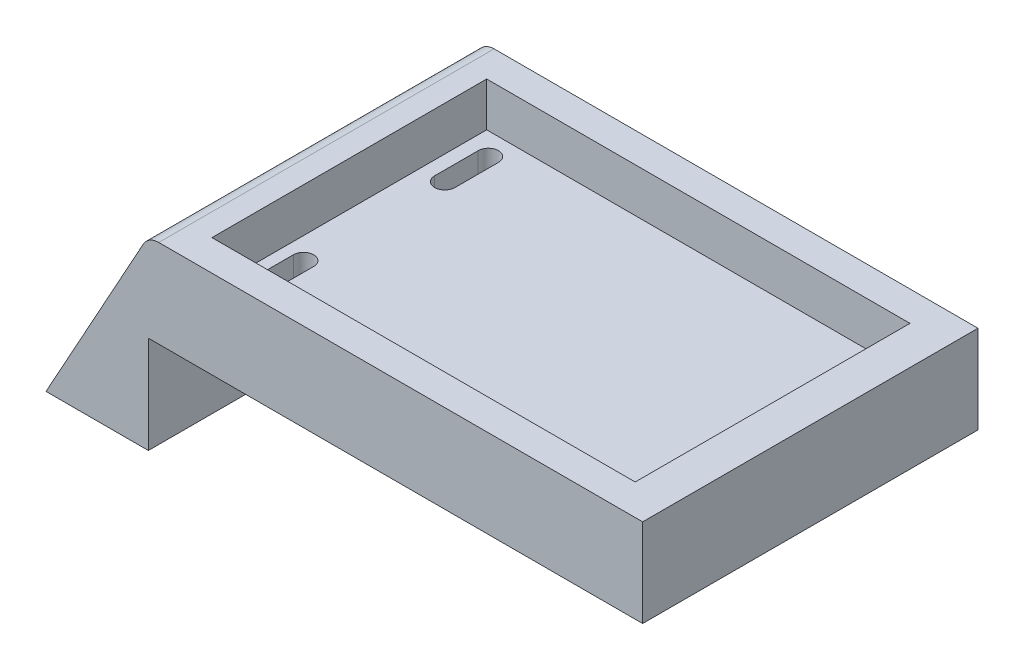
SolidWorks part; units mm, degrees
ref_plane "Front Plane" through (0, 0, 0) normal (0, 0, 1) x (1, 0, 0)
ref_plane "Top Plane" through (0, 0, 0) normal (0, 1, 0) x (1, 0, 0)
ref_plane "Right Plane" through (0, 0, 0) normal (1, 0, 0) x (0, 0, -1)
sketch "Sketch1" plane through (0, 0, 0) normal (0, 1, 0) x (1, 0, 0)
  line L1 (-34.7549, 21.5329) -> (36.5178, 21.5329)
  line L2 (-34.7549, 21.5329) -> (-34.7549, -26.8217)
  line L3 (-34.7549, -26.8217) -> (36.5178, -26.8217)
  line L4 (36.5178, 21.5329) -> (36.5178, -26.8217)
extrude "Boss-Extrude1" add sketch "Sketch1" against normal blind 12.7
sketch "Sketch2" plane through (0, 0, 0) normal (0, 1, 0) x (1, 0, 0)
  line L1 (-30.0271, 17.2356) -> (31.0048, 17.2356)
  line L2 (-30.0271, 17.2356) -> (-30.0271, -22.3816)
  line L3 (-30.0271, -22.3816) -> (31.0048, -22.3816)
  line L4 (31.0048, 17.2356) -> (31.0048, -22.3816)
extrude "Cut-Extrude1" cut sketch "Sketch2" against normal blind 6.35
sketch "Sketch4" plane through (0, 0, 26.8217) normal (0, 0, 1) x (1, 0, 0)
  line L0 (-34.7549, -12.7) -> (-34.7549, -26.7297)
  line L1 (-34.7549, -26.7297) -> (-49.5145, -26.7297)
  line L2 (-49.5145, -26.7297) -> (-34.7549, 0)
  line L3 (-34.7549, 0) -> (-34.7549, -12.7)
extrude "Boss-Extrude2" add sketch "Sketch4" against normal up to surface (48.3546 mm away) up to face at (0.8815, -6.35, -21.5329)
fillet "Fillet1" radius 2.54 1 edges at (-34.7549, 0, 2.6444)
sketch "Sketch5" plane through (0, 0, -21.5329) normal (0, 0, -1) x (-1, 0, 0)
  line L0 (-36.5178, -12.7) -> (34.7549, -12.7) construction
  circle A0 centre (-13.9227, -12.7) radius 7.62
extrude "Cut-Extrude2" cut sketch "Sketch5" against normal blind 2.54
sketch "Sketch7" plane through (0, -6.35, 0) normal (0, 1, 0) x (1, 0, 0)
  line L0 (-26.5747, 14.0285) -> (-26.5747, 7.7385) construction
  line L1 (-25.1099, 14.0285) -> (-25.1099, 7.7385)
  line L2 (-28.0395, 14.0285) -> (-28.0395, 7.7385)
  line L3 (-26.9006, -12.2982) -> (-26.9006, -18.5882) construction
  line L4 (-25.4358, -12.2982) -> (-25.4358, -18.5882)
  line L5 (-28.3654, -12.2982) -> (-28.3654, -18.5882)
  arc A0 (-25.1099, 14.0285) -> (-28.0395, 14.0285) centre (-26.5747, 14.0285) ccw
  arc A1 (-28.0395, 7.7385) -> (-25.1099, 7.7385) centre (-26.5747, 7.7385) ccw
  arc A2 (-25.4358, -12.2982) -> (-28.3654, -12.2982) centre (-26.9006, -12.2982) ccw
  arc A3 (-28.3654, -18.5882) -> (-25.4358, -18.5882) centre (-26.9006, -18.5882) ccw
  point P2 (-26.5747, 10.8835)
  point P10 (-26.9006, -15.4432)
extrude "Cut-Extrude3" cut sketch "Sketch7" against normal up to surface (6.35 mm away) up to face at (6.4496, -12.7, -11.8314)
sketch "Sketch9" plane through (-34.7549, 0, 0) normal (1, 0, 0) x (0, 0, -1)
  line L0 (-2.6444, -26.7297) -> (-2.6444, -13.5483)
  line L1 (21.5329, -26.7297) -> (-26.8217, -26.7297) construction
  line L2 (-2.6444, -13.5483) -> (-0.34, -13.5483)
  line L3 (-0.34, -13.5483) -> (3.5393, -26.7297)
  line L4 (3.5393, -26.7297) -> (-2.6444, -26.7297)
revolve "Cut-Revolve1" cut sketch "Sketch9" angle 180 about L0
